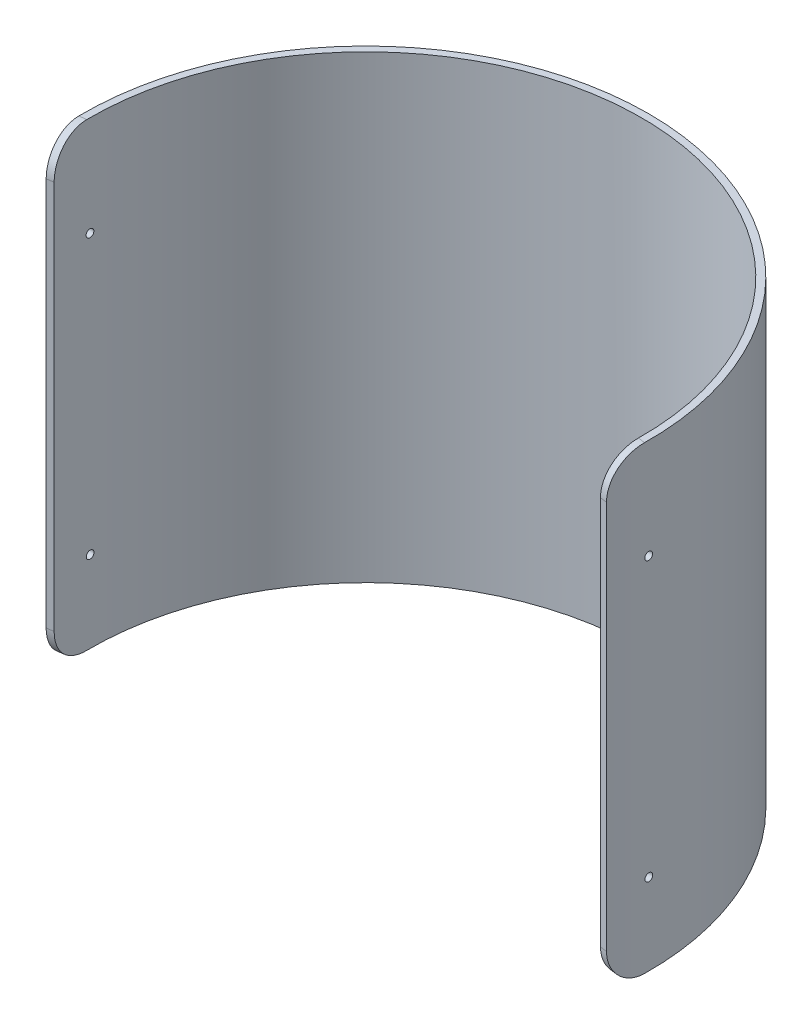
SolidWorks part; units mm, degrees
material "E-Glass Fiber"
ref_plane "Front Plane" through (0, 0, 0) normal (0, 0, 1) x (1, 0, 0)
ref_plane "Top Plane" through (0, 0, 0) normal (0, 1, 0) x (1, 0, 0)
ref_plane "Right Plane" through (0, 0, 0) normal (1, 0, 0) x (0, 0, -1)
sketch "Sketch1" plane through (0, 0, 0) normal (0, 1, 0) x (1, 0, 0)
  circle A0 centre (0, 0) radius 99.06
  circle A1 centre (0, 0) radius 101.6
  dimension "D1" = 203.2
  dimension "D2" = 198.12
extrude "Boss-Extrude1" add sketch "Sketch1" along normal blind 165.1
sketch "Sketch2" plane through (0, 0, 0) normal (0, 1, 0) x (1, 0, 0)
  line L0 (0, 0) -> (-100.6112, -14.14)
  line L1 (0, 0) -> (100.6112, -14.14)
  line L2 (0, 0) -> (0, 101.6) construction
  circle A0 centre (0, 0) radius 101.6 construction
  circle A1 centre (0, 0) radius 101.6
  circle A2 centre (0, 0) radius 99.06 construction
  circle A3 centre (0, 0) radius 99.06
  dimension "D1" = 98
extrude "Cut-Extrude1" cut sketch "Sketch2" along normal blind 165.1 contours A3 L0 A1 L1
fillet "Fillet1" radius 12.7 4 edges at (99.3536, 0, 13.9632) (99.3536, 165.1, 13.9632) (-99.3536, 0, 13.9632) (-99.3536, 165.1, 13.9632)
sketch "Sketch3" plane through (0, 0, 0) normal (1, 0, 0) x (0, 0, -1)
  line L0 (-14.14, 150.8156) -> (-14.14, 2.4359)
  line L1 (-14.14, 152.4) -> (-14.14, 12.7) construction
  line L2 (0, 165.1) -> (0, 0) construction
  line L4 (-1.4527, 0) -> (10.5411, 0)
  line L5 (-1.4527, 0) -> (-1.4527, 177.8)
  line L6 (-1.4527, 177.8) -> (10.5411, 177.8)
  line L7 (10.5411, 0) -> (10.5411, 177.8)
  circle A0 centre (0.084, 147.828) radius 1.397
  circle A1 centre (0.0229, 129.1591) radius 1.397
  circle A2 centre (0.084, 29.1846) radius 1.397
  circle A3 centre (0, 9.8298) radius 1.397
  dimension "D7" = 2.794
  dimension "D8" = 2.794
  dimension "D9" = 2.794
  dimension "D10" = 2.794
  dimension "D1" = 29.972
  dimension "D2" = 14.224
  dimension "D3" = 177.8
  dimension "D4" = 18.669
  dimension "D5" = 137.9982
  dimension "D6" = 19.3548
extrude "Cut-Extrude2" cut sketch "Sketch3" against normal through all both and the other way through all contours A2 | A1
sketch "Sketch4" plane through (0, 0, 0) normal (0, 0, 1) x (1, 0, 0)
  circle A2 centre (0, 20.32) radius 9.525
  dimension "D1" = 19.05
  dimension "D2" = 20.32
extrude "Cut-Extrude3" cut sketch "Sketch4" against normal through all
